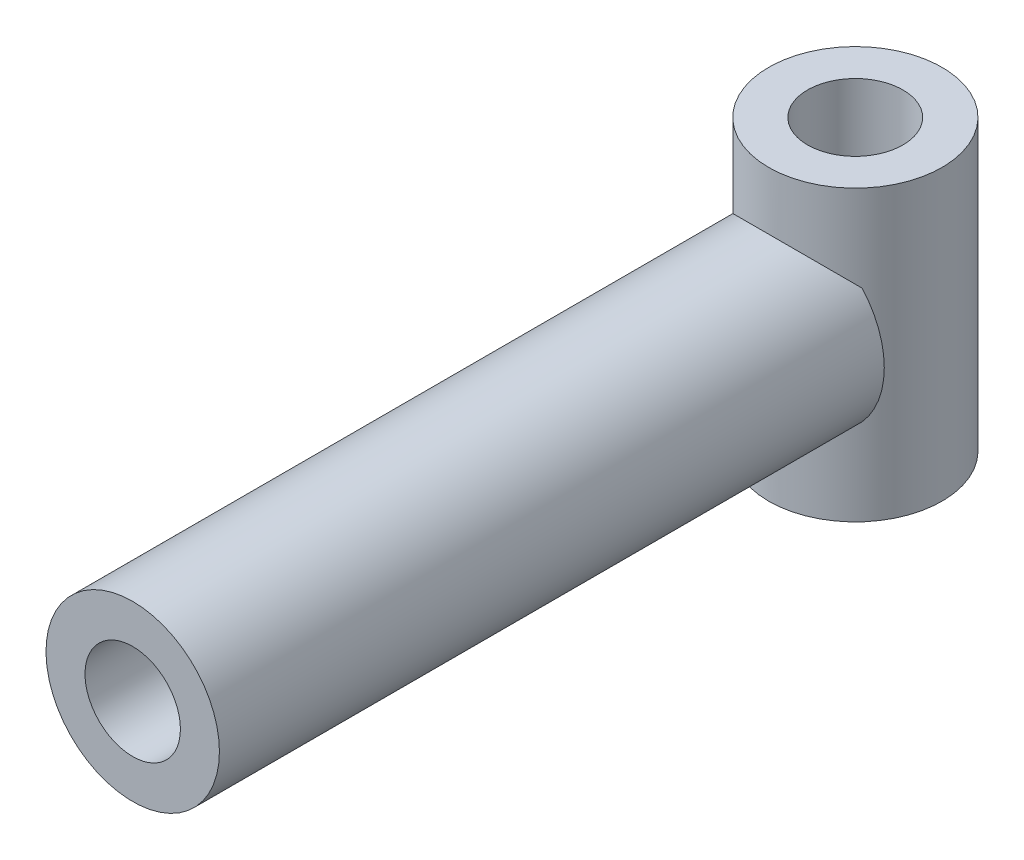
SolidWorks part; units mm, degrees
ref_plane "Přední rovina" through (0, 0, 0) normal (0, 0, 1) x (1, 0, 0)
ref_plane "Horní rovina" through (0, 0, 0) normal (0, 1, 0) x (1, 0, 0)
ref_plane "Pravá rovina" through (0, 0, 0) normal (1, 0, 0) x (0, 0, -1)
sketch "Skica1" plane through (0, 0, 0) normal (0, 0, 1) x (1, 0, 0)
  circle A0 centre (0, 0) radius 3
  dimension "D1" = 6
extrude "Přidat vysunutím1" add sketch "Skica1" along normal blind 23
sketch "Skica2" plane through (0, 0, 23) normal (0, 0, 1) x (1, 0, 0)
  circle A0 centre (0, 0) radius 1.65
  dimension "D1" = 3.3
extrude "Odebrat vysunutím1" cut sketch "Skica2" against normal blind 20
sketch "Skica3" plane through (0, 0, 0) normal (0, 1, 0) x (1, 0, 0)
  circle A0 centre (0, 2) radius 3
  dimension "D1" = 6
  dimension "D2" = 2
extrude "Přidat vysunutím2" add sketch "Skica3" along normal mid plane 10
sketch "Skica4" plane through (0, 5, 0) normal (0, 1, 0) x (1, 0, 0)
  circle A0 centre (0, 1.9958) radius 1.65
  dimension "D1" = 3.3
extrude "Odebrat vysunutím2" cut sketch "Skica4" against normal blind 10
